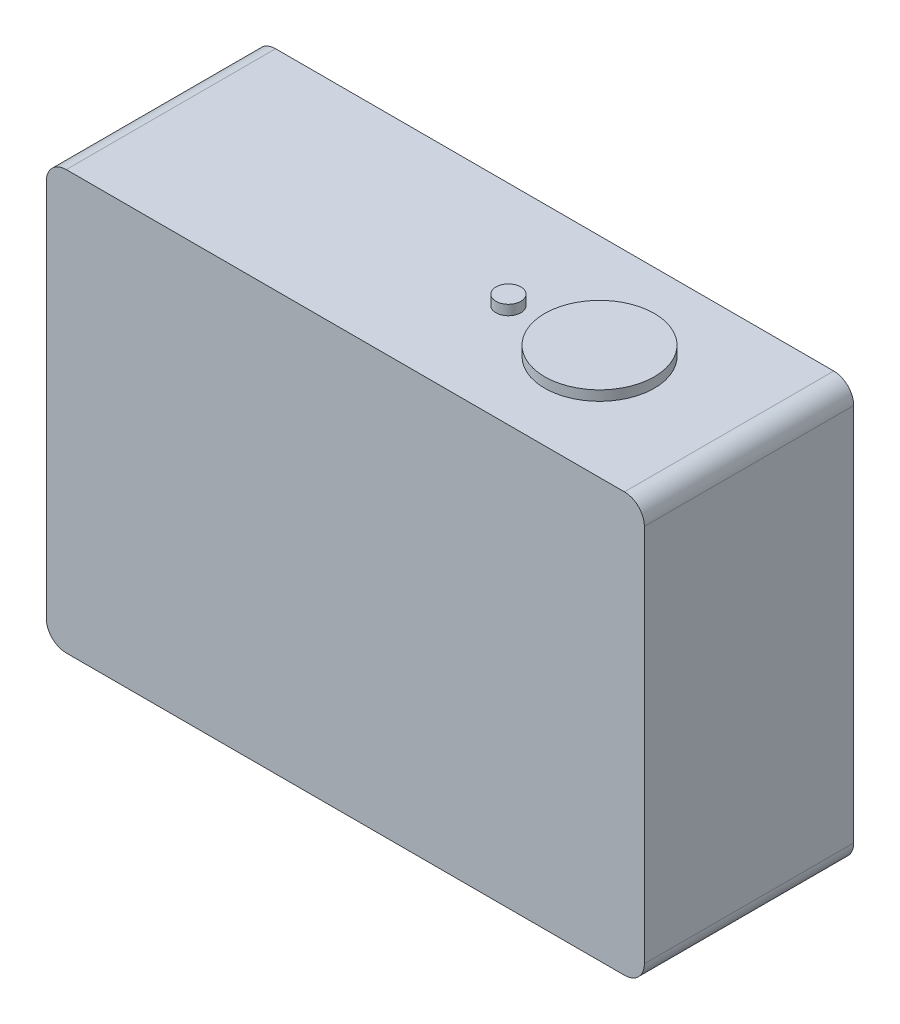
SolidWorks part; units mm, degrees
ref_plane "Front Plane" through (0, 0, 0) normal (0, 0, 1) x (1, 0, 0)
ref_plane "Top Plane" through (0, 0, 0) normal (0, 1, 0) x (1, 0, 0)
ref_plane "Right Plane" through (0, 0, 0) normal (1, 0, 0) x (0, 0, -1)
sketch "Sketch1" plane through (0, 0, 0) normal (0, 0, 1) x (1, 0, 0)
  line L1 (-30, -21) -> (30, -21)
  line L2 (-30, -21) -> (-30, 21)
  line L3 (-30, 21) -> (30, 21)
  line L4 (30, -21) -> (30, 21)
  line L5 (-30, -21) -> (30, 21) construction
  line L6 (-30, 21) -> (30, -21) construction
  point P0 (0, 0)
  dimension "D1" = 60
  dimension "D2" = 42
extrude "Boss-Extrude1" add sketch "Sketch1" along normal blind 21
fillet "Fillet1" radius 2 4 edges at (-30, -21, 10.5) (30, -21, 10.5) (30, 21, 10.5) (-30, 21, 10.5)
sketch "Sketch2" plane through (0, 0, 0) normal (0, 0, -1) x (-1, 0, 0)
  line L0 (-30, -19) -> (-30, 19) construction
  line L1 (-28, 21) -> (28, 21) construction
  circle A1 centre (13, 0) radius 11.8753
  circle A2 centre (13, 0) radius 8.8729
  dimension "D2" = 43
  dimension "D3" = 21
extrude "Boss-Extrude2" add sketch "Sketch2" along normal blind 7.5
sketch "Sketch3" plane through (0, 0, 0) normal (0, 0, 1) x (1, 0, 0)
  line L0 (30, -19) -> (30, 19) construction
  circle A0 centre (15, 0) radius 7.4192
  dimension "D1" = 15
extrude "Boss-Extrude3" add sketch "Sketch3" against normal blind 2
sketch "Sketch4" plane through (0, 21, 0) normal (0, 1, 0) x (1, 0, 0)
  line L0 (28, 0) -> (-28, 0) construction
  line L1 (30, 0) -> (30, -21) construction
  circle A0 centre (15, -10.5) radius 5.5
  dimension "D2" = 11
  dimension "D1" = 10.5
  dimension "D3" = 15
extrude "Boss-Extrude5" add sketch "Sketch4" along normal blind 1
sketch "Sketch5" plane through (0, 21, 0) normal (0, 1, 0) x (1, 0, 0)
  line L0 (30, 0) -> (30, -21) construction
  circle A0 centre (6, -10.6399) radius 1.25
  dimension "D1" = 2.5
  dimension "D2" = 24
extrude "Boss-Extrude6" add sketch "Sketch5" along normal blind 1
sketch "Sketch7" plane through (0, 0, 0) normal (0, 0, -1) x (-1, 0, 0)
  circle A2 centre (13, 0) radius 8.8729
extrude "Boss-Extrude8" add sketch "Sketch7" along normal blind 4 contours A2
